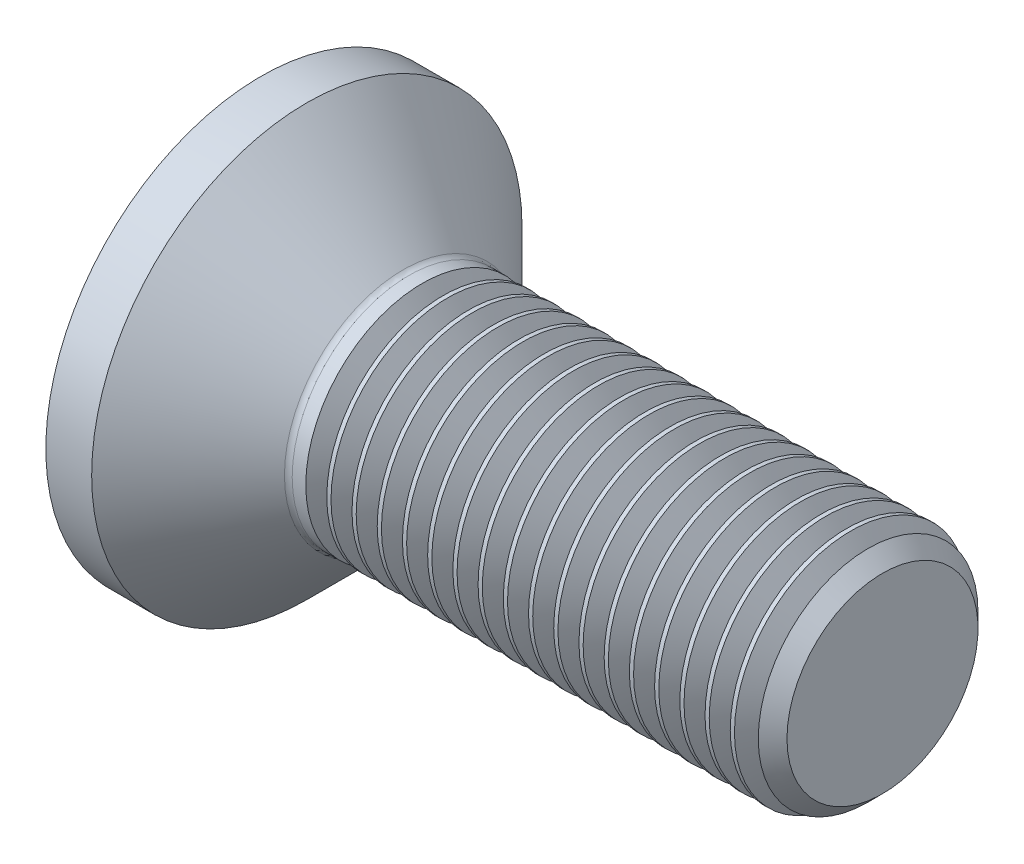
SolidWorks part; units mm, degrees
ref_plane "Front" through (0, 0, 0) normal (0, 0, 1) x (1, 0, 0)
ref_plane "Top" through (0, 0, 0) normal (0, 1, 0) x (1, 0, 0)
ref_plane "Right" through (0, 0, 0) normal (1, 0, 0) x (0, 0, -1)
sketch "Sketch1" plane through (0, 0, 0) normal (0, 0, 1) x (1, 0, 0)
  line L0 (0, 0) -> (0, 3.36)
  line L1 (0, 3.36) -> (1.86, 1.5)
  line L2 (1.86, 1.5) -> (8, 1.5)
  line L3 (8, 1.5) -> (8, 0)
  line L4 (8, 0) -> (0, 0)
  line L5 (-0.5871, 0) -> (5.4927, 0) construction
  dimension "l" = 8
  dimension "k" = 1.86
  dimension "d" = 3
  dimension "D1" = 45
revolve "Base" add sketch "Sketch1" angle 360 about L5
cosmetic thread "ThreadCosmetic1" [suppressed] parameters "b"=6, "D2"=2.459
sketch "Sketch2" plane through (0, 0, 0) normal (1, 0, 0) x (0, 0, -1)
  line L1 (1.1547, 0) -> (0.5774, 1)
  line L2 (0.5774, 1) -> (-0.5774, 1)
  line L3 (-0.5774, 1) -> (-1.1547, 0)
  line L4 (-1.1547, 0) -> (-0.5774, -1)
  line L5 (-0.5774, -1) -> (0.5774, -1)
  line L6 (0.5774, -1) -> (1.1547, 0)
  circle A0 centre (0, 0) radius 1 construction
  dimension "s" = 2
extrude "HexagonSocket" cut sketch "Sketch2" along normal blind 1.1
sketch "Sketch3" plane through (0, 0, 0) normal (0, 0, 1) x (1, 0, 0)
  line L0 (-0.4391, 0) -> (4.425, 0) construction
  line L1 (1.1, 0) -> (1.1, -1) construction
  line L2 (1.1, 1) -> (1.6774, 0)
  line L3 (1.6774, 0) -> (1.1, -1) construction
  line L4 (1.1, 1) -> (1.1, 0)
  line L5 (1.1, 0) -> (1.6774, 0)
  line L7 (1.1, 1) -> (1.1, 0) construction
  dimension "D1" = 120
revolve "Cut-Revolve1" cut sketch "Sketch3" angle 360 about L0
fillet "HeadFillet" radius 0.1 1 edges at (1.86, 0, 1.5)
chamfer "Chamfer" distance 0.2705 angle 45 1 edges at (8, 0, 1.5)
sketch "Sketch4" plane through (0, 0, 0) normal (0, 1, 0) x (1, 0, 0)
  line L0 (11.8531, 0) -> (-2.694, 0) construction
  line L1 (-2, 7.77) -> (3, 7.77)
  line L2 (-2, 7.77) -> (-2, 2.77)
  line L3 (-2, 2.77) -> (3, 2.77)
  line L4 (3, 7.77) -> (3, 2.77)
  line L5 (0, 3.36) -> (0, -3.36) construction
  dimension "dk" = 5.54
  dimension "D2" = 2
  dimension "D3" = 5
  dimension "D4" = 5
revolve "Cut-Revolve2" cut sketch "Sketch4" angle 360 about L0
sketch "Sketch5" plane through (0, 0, 0) normal (0, 0, 1) x (1, 0, 0)
  line L0 (7.7295, 1.2657) -> (7.8648, 1.5)
  line L1 (7.8648, 1.5) -> (7.8648, 1.7705)
  line L2 (7.8648, 1.7705) -> (7.5943, 1.7705)
  line L3 (7.5943, 1.7705) -> (7.5943, 1.5)
  line L4 (7.5943, 1.5) -> (7.7295, 1.2657)
  line L5 (0, 0) -> (10.6885, 0) construction
  line L6 (7.7295, 1.5) -> (7.7295, -1.5) construction
  dimension "D1" = 3
  dimension "D2" = 0.2705
revolve "Cut-Revolve10" cut sketch "Sketch5" angle 360 about L5
pattern_linear "LPattern10" count 18 spacing 0.3246 along (-1, 0, 0) of "Cut-Revolve10"
equation "\"D1@Chamfer\" = (  \"d@Sketch1\" - \"D2@ThreadCosmetic1\" )  / 2"
equation "\"D1@Sketch5\" = \"d@Sketch1\""
equation "\"D2@Sketch5\" =  ( \"d@Sketch1\" - \"D2@ThreadCosmetic1\" )  / 2"
equation "\"D3@LPattern10\" = \"D2@Sketch5\" * 1.2"
equation "\"D1@LPattern10\" = \"b@ThreadCosmetic1\" / \"D3@LPattern10\""
